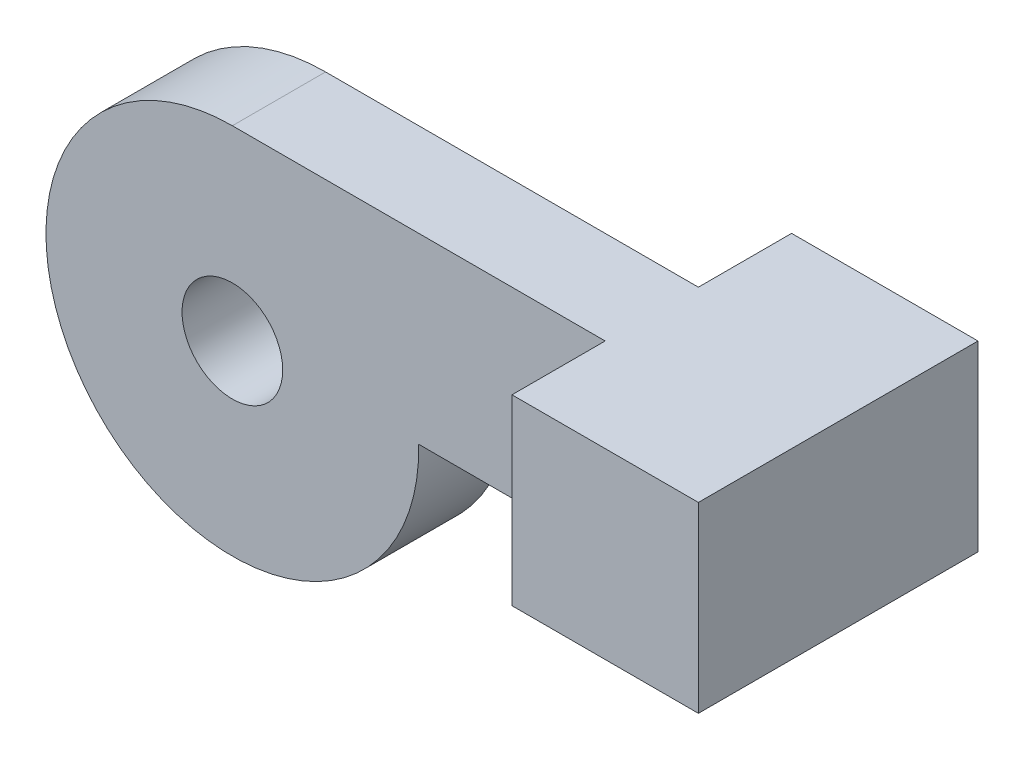
SolidWorks part; units mm, degrees
ref_plane "Front Plane" through (0, 0, 0) normal (0, 0, 1) x (1, 0, 0)
ref_plane "Top Plane" through (0, 0, 0) normal (0, 1, 0) x (1, 0, 0)
ref_plane "Right Plane" through (0, 0, 0) normal (1, 0, 0) x (0, 0, -1)
sketch "Sketch1" plane through (0, 0, 0) normal (0, 0, 1) x (1, 0, 0)
  line L5 (0, 12.7) -> (38.1, 12.7)
  line L6 (38.1, 12.7) -> (38.1, 0.254)
  line L7 (38.1, 0.254) -> (12.6975, 0.254)
  circle A2 centre (0, 0) radius 3.429
  arc A3 (0, 12.7) -> (12.6975, 0.254) centre (0, 0) ccw
  dimension "D3" = 6.858
  dimension "D5" = 25.4
  dimension "D2" = 0.254
  dimension "D4" = 38.1
extrude "Boss-Extrude1" add sketch "Sketch1" along normal mid plane 6.35
sketch "Sketch2" plane through (0, 0, 0) normal (0, 0, 1) x (1, 0, 0)
  line L0 (12.6975, 0.254) -> (38.1, 0.254) construction
  line L1 (38.1, 12.7) -> (25.4, 12.7)
  line L2 (38.1, 12.7) -> (38.1, 0.254)
  line L3 (38.1, 0.254) -> (25.4, 0.254)
  line L4 (25.4, 12.7) -> (25.4, 0.254)
  dimension "D1" = 12.7
extrude "Boss-Extrude2" add sketch "Sketch2" along normal mid plane 19.05
equation "\"tightTol\"= 0.005in"
equation "\"normTol\"= 0.01in"
equation "\"looseTol\"= 0.02in"
equation "\"D2@Sketch1\"=\"normTol\""
equation "\"D3@Sketch1\"=0.25+\"looseTol\""
equation "\"D1\"= \"looseTol\" + 0.250000in"
